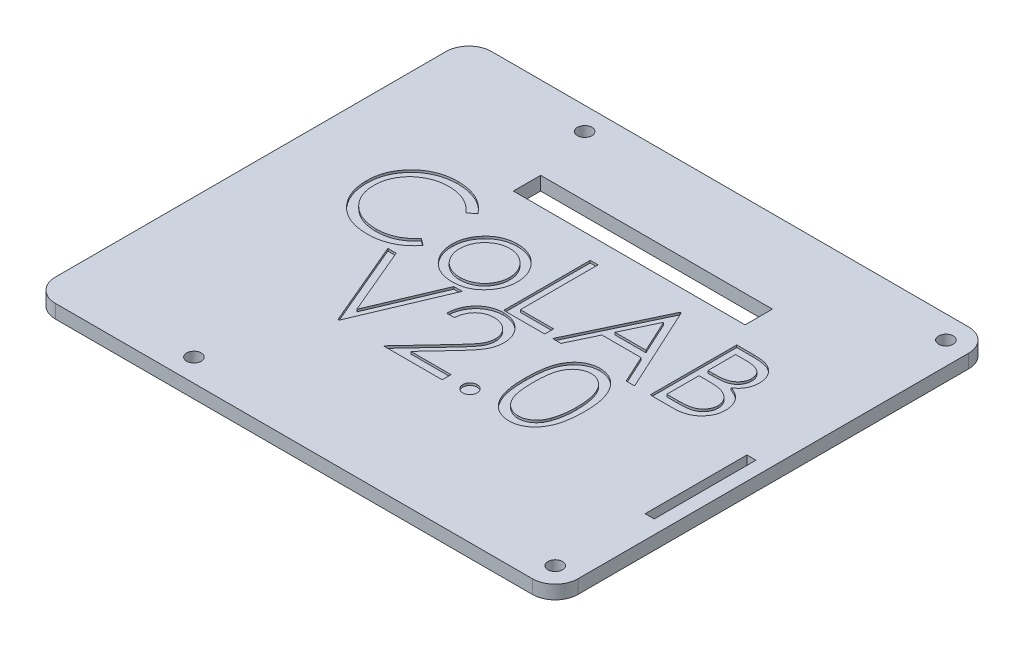
SolidWorks part; units mm, degrees
ref_plane "Front" through (0, 0, 0) normal (0, 0, 1) x (1, 0, 0)
ref_plane "Top" through (0, 0, 0) normal (0, 1, 0) x (1, 0, 0)
ref_plane "Right" through (0, 0, 0) normal (1, 0, 0) x (0, 0, -1)
sketch "Sketch1" plane through (0, 0, 0) normal (0, 1, 0) x (1, 0, 0)
  line L1 (5, 0) -> (110, 0)
  line L2 (0, 5) -> (0, 91)
  line L3 (5, 96) -> (110, 96)
  line L4 (115, 5) -> (115, 91)
  arc A0 (5, 0) -> (0, 5) centre (5, 5) cw
  arc A1 (110, 0) -> (115, 5) centre (110, 5) ccw
  arc A2 (110, 96) -> (115, 91) centre (110, 91) cw
  arc A3 (0, 91) -> (5, 96) centre (5, 91) cw
  point P7 (0, 0)
  point P10 (115, 0)
  point P15 (0, 96)
  dimension "D3" = 5
  dimension "D1" = 96
  dimension "D2" = 115
extrude "Boss-Extrude1" add sketch "Sketch1" along normal blind 3
sketch "Sketch2" plane through (0, 3, 0) normal (0, 1, 0) x (1, 0, 0)
  line L0 (0, 48) -> (115, 48) construction
  line L1 (0, 91) -> (0, 5) construction
  line L2 (115, 5) -> (115, 91) construction
  line L3 (0, 28) -> (115, 28) construction
  text T0 "CoLAB" font "Century Gothic" height in points 72
  text T1 "V2.0" font "Century Gothic" height in points 72
  dimension "D1" = 20
extrude "Cut-Extrude1" cut sketch "Sketch2" against normal blind 0.5
sketch "Sketch3" plane through (0, 0, 0) normal (0, -1, 0) x (1, 0, 0)
  line L0 (0, -91) -> (0, -5) construction
  line L1 (110, -96) -> (5, -96) construction
  line L2 (0, -48) -> (115, -48) construction
  line L3 (115, -5) -> (115, -91) construction
  circle A0 centre (30.5, -91) radius 1.6
  circle A1 centre (110, -91) radius 1.6
  arc A2 (110, -96) -> (115, -91) centre (110, -91) ccw construction
  circle A3 centre (110, -5) radius 1.6
  circle A4 centre (30.5, -5) radius 1.6
  dimension "D1" = 30.5
  dimension "D3" = 3.2
  dimension "D2" = 5
extrude "Cut-Extrude2" cut sketch "Sketch3" against normal through all both and the other way through all
sketch "Sketch5" plane through (0, 3, 0) normal (0, 1, 0) x (1, 0, 0)
  line L0 (115, 5) -> (115, 91) construction
  line L1 (115, 47.2) -> (112, 47.2)
  line L2 (115, 47.2) -> (115, 24.8)
  line L3 (115, 24.8) -> (112, 24.8)
  line L4 (112, 47.2) -> (112, 24.8)
  line L5 (5, 0) -> (110, 0) construction
  line L7 (112, 47.2) -> (110, 47.2)
  line L8 (112, 47.2) -> (112, 24.8)
  line L9 (112, 24.8) -> (110, 24.8)
  line L10 (110, 47.2) -> (110, 24.8)
  dimension "D1" = 22.4
  dimension "D2" = 24.8
  dimension "D3" = 3
  dimension "D4" = 2
extrude "Cut-Extrude3" cut sketch "Sketch5" against normal through all both and the other way through all contours L7 L10 L9 L4
sketch "Sketch6" plane through (0, 0, 0) normal (0, -1, 0) x (1, 0, 0)
  line L0 (110, -96) -> (5, -96) construction
  line L1 (115, -5) -> (115, -91) construction
  circle A0 centre (92, -60) radius 1.45
  circle A1 centre (80, -23) radius 1.45
  circle A2 centre (55, -58.7) radius 1.45
  circle A3 centre (31.14, -20.6) radius 1.45
  circle A4 centre (12.34, -37.36) radius 1.45
  circle A5 centre (80, -23) radius 3.5
  circle A6 centre (92, -60) radius 3.5
  circle A7 centre (55, -58.7) radius 3.5
  circle A8 centre (12.34, -37.36) radius 3.5
  circle A9 centre (31.14, -20.6) radius 3.5
  dimension "D1" = 2.9
  dimension "D12" = 7
  dimension "D13" = 7
  dimension "D14" = 7
  dimension "D15" = 7
  dimension "D16" = 7
  dimension "D2" = 36
  dimension "D3" = 23
  dimension "D4" = 37
  dimension "D5" = 35
  dimension "D6" = 25
  dimension "D7" = 23.86
  dimension "D8" = 38.1
  dimension "D9" = 16.76
  dimension "D10" = 18.8
  dimension "D11" = 1.3
extrude "Boss-Extrude2" add sketch "Sketch6" along normal blind 5 contours A8 A4 | A9 A3 | A5 A1 | A7 A2 | A6 A0
sketch "Sketch7" plane through (0, 3, 0) normal (0, 1, 0) x (1, 0, 0)
  line L0 (115, 5) -> (115, 91) construction
  line L1 (34, 77.8) -> (85, 77.8)
  line L2 (34, 77.8) -> (34, 71.8)
  line L3 (34, 71.8) -> (85, 71.8)
  line L4 (85, 77.8) -> (85, 71.8)
  line L5 (0, 91) -> (0, 5) construction
  line L6 (110, 96) -> (5, 96) construction
  dimension "D1" = 30
  dimension "D2" = 34
  dimension "D3" = 18.2
  dimension "D4" = 6
extrude "Cut-Extrude4" cut sketch "Sketch7" against normal through all both and the other way through all
